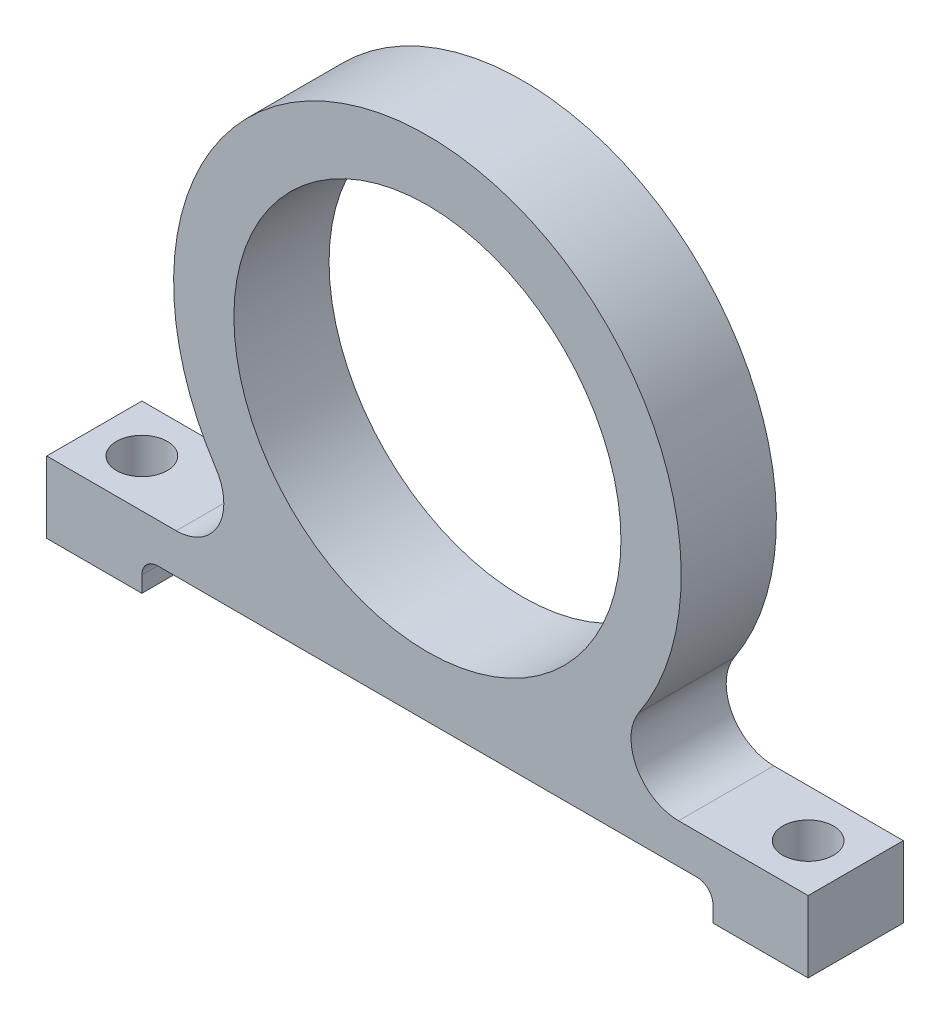
SolidWorks part; units mm, degrees
ref_plane "Front Plane" through (0, 0, 0) normal (0, 0, 1) x (1, 0, 0)
ref_plane "Top Plane" through (0, 0, 0) normal (0, 1, 0) x (1, 0, 0)
ref_plane "Right Plane" through (0, 0, 0) normal (1, 0, 0) x (0, 0, -1)
sketch "Sketch1" plane through (0, 0, 0) normal (0, 0, 1) x (1, 0, 0)
  line L0 (18, -16) -> (-18, -16)
  line L1 (-18, -16) -> (-18, -18)
  line L2 (-18, -18) -> (-24, -18)
  line L3 (-24, -18) -> (-24, -13.5)
  line L4 (-24, -13.5) -> (-8.5878, -13.5)
  line L5 (0, -13.5) -> (0, 12.2) construction
  line L6 (24, -18) -> (24, -13.5)
  line L7 (18, -18) -> (24, -18)
  line L8 (18, -16) -> (18, -18)
  line L9 (8.5878, -13.5) -> (24, -13.5)
  circle A0 centre (0, 0) radius 12.2
  arc A1 (8.5878, -13.5) -> (-8.5878, -13.5) centre (0, 0) ccw
  point P11 (0, -12.2)
  dimension "D1" = 24.4
  dimension "D2" = 32
  dimension "D3" = 36
  dimension "D4" = 48
  dimension "D5" = 2
extrude "Boss-Extrude1" add sketch "Sketch1" along normal blind 6
fillet "Fillet1" radius 3 2 edges at (8.5878, -13.5, 3) (-8.5878, -13.5, 3)
fillet "Fillet2" radius 1 2 edges at (18, -16, 3) (-18, -16, 3)
sketch "Sketch4" plane through (0, -13.5, 0) normal (0, 1, 0) x (1, 0, 0)
  line L0 (-15.8351, -6) -> (-24, -6) construction
  line L1 (-24, -6) -> (-24, 0) construction
  line L2 (24, -6) -> (15.8351, -6) construction
  line L3 (24, -6) -> (24, 0) construction
  point P0 (-21, -3)
  point P2 (21, -3)
  dimension "D1" = 3
  dimension "D2" = 3
  dimension "D3" = 3
  dimension "D4" = 3
hole_wizard "Ø3.0mm Dowel Hole1" positions "Sketch4" profile "Sketch5" hole size "Ø3.0" standard "ANSI Metric" end condition through all
sketch "Sketch5" plane through (-21, -13.5, 3) normal (1, 0, 0) x (0, 0, 1)
  line L0 (0, 0) -> (0, 4.5)
  line L1 (0, 4.5) -> (1.6, 4.5)
  line L2 (1.6, 4.5) -> (1.6, 0)
  line L5 (1.6, 0) -> (0, 0)
  line L11 (0, -6.35) -> (0, 107.95) construction
  dimension "Thru Hole Dia." = 3.2
  dimension "Thru Hole Depth" = 4.5
